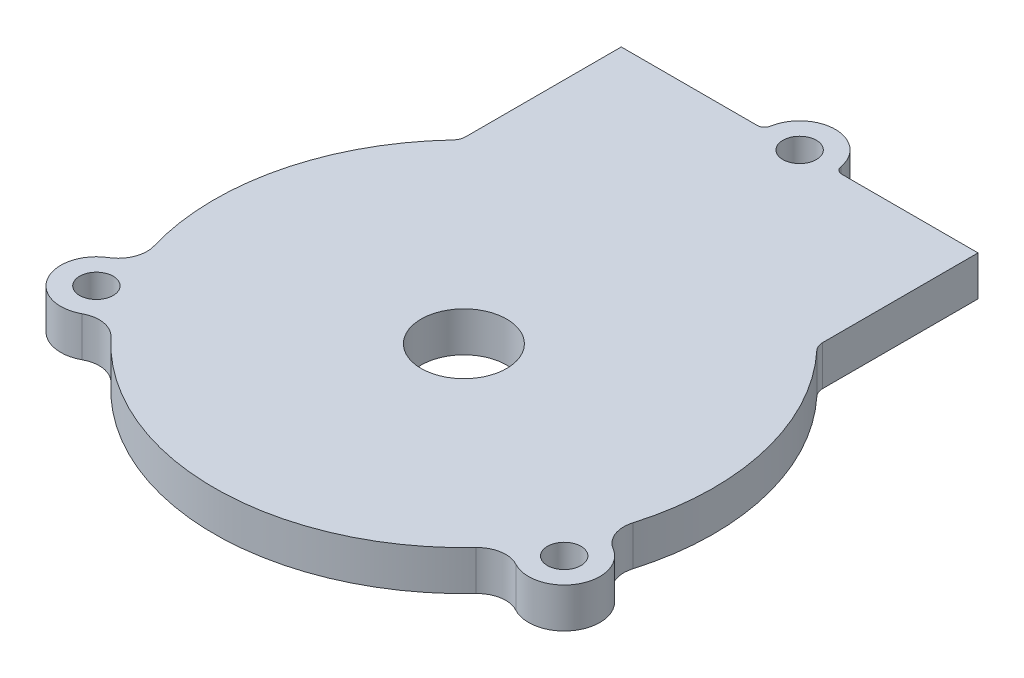
SolidWorks part; units mm, degrees
ref_plane "Front Plane" through (0, 0, 0) normal (0, 0, 1) x (1, 0, 0)
ref_plane "Top Plane" through (0, 0, 0) normal (0, 1, 0) x (1, 0, 0)
ref_plane "Right Plane" through (0, 0, 0) normal (1, 0, 0) x (0, 0, -1)
sketch "Sketch1" plane through (0, 0, 0) normal (0, 1, 0) x (1, 0, 0)
  line L0 (0, 0) -> (65.57, 0) construction
  line L2 (32.785, 0) -> (32.785, 24.2952) construction
  line L3 (0, 0) -> (32.785, 65.7829) construction
  line L5 (65.57, 0) -> (32.785, 65.7829) construction
  line L7 (32.785, 0) -> (32.785, 18.8) construction
  line L10 (32.785, 65.7829) -> (57.785, 65.7829) construction
  line L11 (32.785, 65.7829) -> (32.785, 58.7829) construction
  line L12 (32.785, 58.7829) -> (57.785, 58.7829) construction
  line L13 (57.785, 65.7829) -> (57.785, 58.7829) construction
  line L15 (57.785, 65.7829) -> (7.785, 65.7829)
  line L16 (57.785, 65.7829) -> (57.785, 40.7829)
  line L17 (57.785, 40.7829) -> (7.785, 40.7829)
  line L18 (7.785, 65.7829) -> (7.785, 40.7829)
  circle A0 centre (32.785, 18.7243) radius 35
  circle A1 centre (65.57, 0) radius 5
  circle A2 centre (0, 0) radius 5
  circle A3 centre (32.785, 65.7829) radius 5
  circle A4 centre (32.785, 18.7243) radius 6
  point P7 (32.785, 0)
  point P21 (32.785, 18.7243)
  dimension "D1" = 7
  dimension "D2" = 25
  dimension "D3" = 50
  dimension "D4" = 25
extrude "Boss-Extrude2" add sketch "Sketch1" along normal blind 5.588 contours A1 | A2 | A0 | A3 | A4 | L18 L17 L16 L15
hole_wizard "Ø4.7 (4.7) Diameter Hole1" positions "Sketch16" profile "Sketch17" hole size "Ø4.7" standard "ANSI Metric" end condition through all
sketch "Sketch16" plane through (0, 5.588, 0) normal (0, 1, 0) x (1, 0, 0)
  point P0 (0, 0)
  point P3 (65.57, 0)
  point P6 (32.785, 65.7829)
sketch "Sketch17" plane through (0, 5.588, 0) normal (1, 0, 0) x (0, 0, 1)
  line L0 (0, 0) -> (0, 5.588)
  line L1 (0, 5.588) -> (2.35, 5.588)
  line L2 (2.35, 5.588) -> (2.35, 0)
  line L5 (2.35, 0) -> (0, 0)
  line L11 (0, -6.35) -> (0, 107.95) construction
  dimension "Thru Hole Dia." = 4.7
  dimension "Thru Hole Depth" = 5.588
fillet "Fillet1" radius 1 1 edges at (27.785, 2.794, -65.7829)
fillet "Fillet2" radius 1 1 edges at (37.785, 2.794, -65.7829)
fillet "Fillet6" radius 4 1 edges at (0.6037, 2.794, -4.9634)
fillet "Fillet7" radius 4 1 edges at (4.5817, 2.794, 2.0019)
fillet "Fillet8" radius 4 2 edges at (64.9663, 2.794, -4.9634) (60.9883, 2.794, 2.0019)
fillet "Fillet9" radius 2 1 edges at (57.785, 2.794, -43.2192)
fillet "Fillet10" radius 2 1 edges at (7.785, 2.794, -43.2192)
